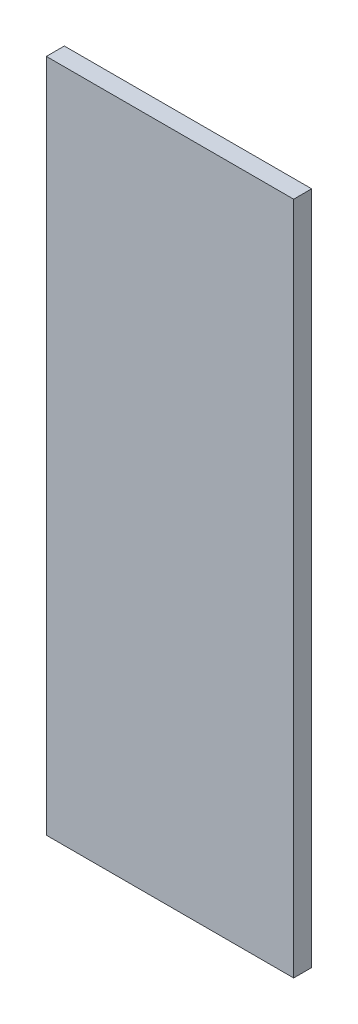
SolidWorks part; units mm, degrees
ref_plane "Front Plane" through (0, 0, 0) normal (0, 0, 1) x (1, 0, 0)
ref_plane "Top Plane" through (0, 0, 0) normal (0, 1, 0) x (1, 0, 0)
ref_plane "Right Plane" through (0, 0, 0) normal (1, 0, 0) x (0, 0, -1)
sketch "Sketch1" plane through (0, 0, 0) normal (0, 0, 1) x (1, 0, 0)
  line L1 (0, 0) -> (55, 0)
  line L2 (0, 0) -> (0, 150)
  line L3 (0, 150) -> (55, 150)
  line L4 (55, 0) -> (55, 150)
  dimension "D1" = 150
  dimension "D2" = 55
extrude "Boss-Extrude1" add sketch "Sketch1" along normal blind 4
